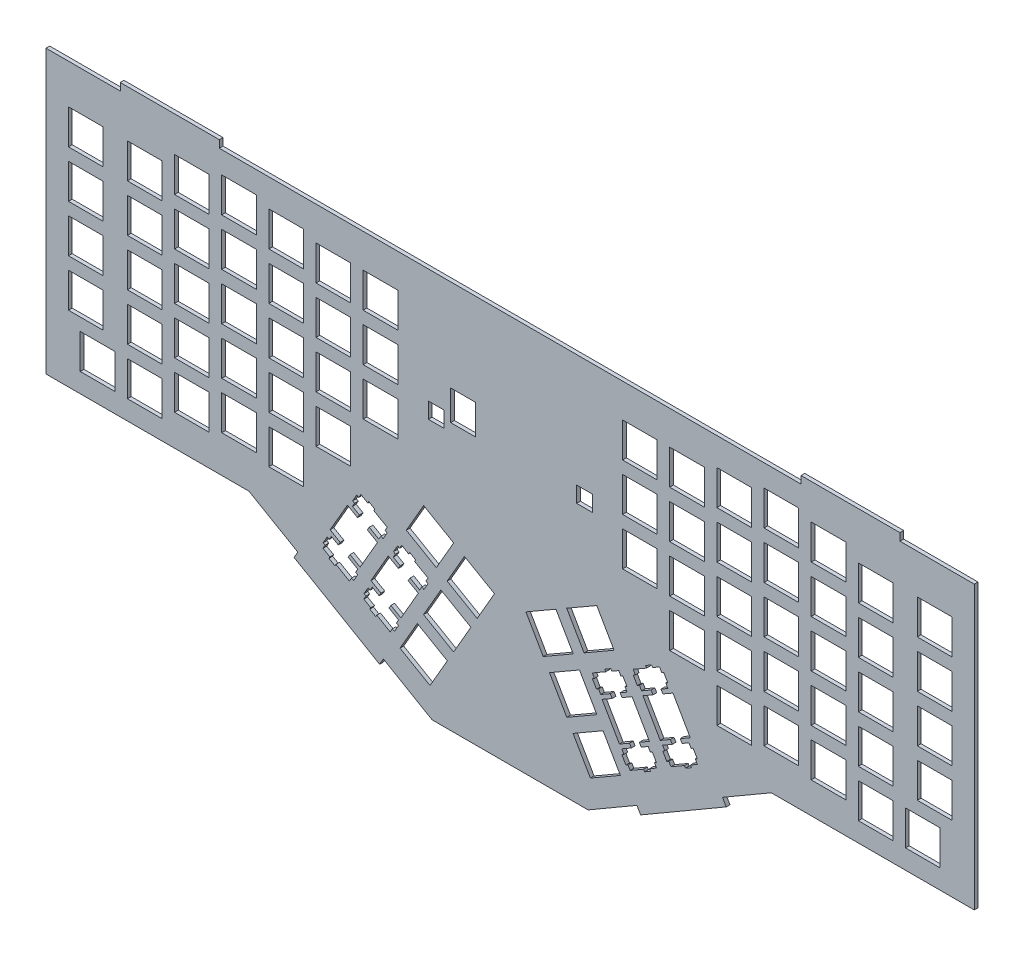
SolidWorks part; units mm, degrees
ref_plane "Front Plane" through (0, 0, 0) normal (0, 0, 1) x (1, 0, 0)
ref_plane "Top Plane" through (0, 0, 0) normal (0, 1, 0) x (1, 0, 0)
ref_plane "Right Plane" through (0, 0, 0) normal (1, 0, 0) x (0, 0, -1)
sketch "Model" plane through (0, 0, 0) normal (0, 0, 1) x (1, 0, 0)
  line L0 (0.0951, 142.78) -> (371.57, 142.78)
  line L1 (371.57, 142.78) -> (371.57, 0.2467)
  line L2 (371.57, 0.2467) -> (0.0951, 0.2467)
  line L3 (0.0951, 0.2467) -> (0.0951, 142.78)
  line L4 (141.314, 10.6977) -> (153.439, 3.6973)
  line L5 (153.439, 3.6973) -> (160.438, 15.8213)
  line L6 (160.438, 15.8213) -> (148.314, 22.8217)
  line L7 (148.314, 22.8217) -> (141.314, 10.6977)
  line L8 (211.224, 15.8213) -> (218.225, 3.6973)
  line L9 (218.225, 3.6973) -> (230.35, 10.6977)
  line L10 (230.35, 10.6977) -> (223.35, 22.8217)
  line L11 (223.35, 22.8217) -> (211.224, 15.8213)
  line L12 (141.126, 45.533) -> (140.33, 45.992)
  line L13 (140.33, 45.992) -> (138.679, 43.1341)
  line L14 (138.679, 43.1341) -> (139.477, 42.6752)
  line L15 (139.477, 42.6752) -> (138.614, 41.1812)
  line L16 (138.614, 41.1812) -> (141.412, 39.5661)
  line L17 (141.412, 39.5661) -> (140.648, 38.2461)
  line L18 (140.648, 38.2461) -> (136.579, 40.5955)
  line L19 (136.579, 40.5955) -> (129.578, 28.4716)
  line L20 (129.578, 28.4716) -> (133.649, 26.1221)
  line L21 (133.649, 26.1221) -> (132.887, 24.8006)
  line L22 (132.887, 24.8006) -> (130.09, 26.4156)
  line L23 (130.09, 26.4156) -> (129.227, 24.9218)
  line L24 (129.227, 24.9218) -> (128.429, 25.3821)
  line L25 (128.429, 25.3821) -> (126.78, 22.524)
  line L26 (126.78, 22.524) -> (127.576, 22.0638)
  line L27 (127.576, 22.0638) -> (126.715, 20.57)
  line L28 (126.715, 20.57) -> (129.512, 18.9549)
  line L29 (129.512, 18.9549) -> (129.099, 18.2411)
  line L30 (129.099, 18.2411) -> (131.524, 16.841)
  line L31 (131.524, 16.841) -> (131.936, 17.5548)
  line L32 (131.936, 17.5548) -> (137.367, 14.4198)
  line L33 (137.367, 14.4198) -> (138.228, 15.9136)
  line L34 (138.228, 15.9136) -> (139.077, 15.423)
  line L35 (139.077, 15.423) -> (140.728, 18.2811)
  line L36 (140.728, 18.2811) -> (139.879, 18.773)
  line L37 (139.879, 18.773) -> (140.742, 20.2654)
  line L38 (140.742, 20.2654) -> (136.871, 22.5006)
  line L39 (136.871, 22.5006) -> (137.633, 23.8221)
  line L40 (137.633, 23.8221) -> (141.702, 21.4712)
  line L41 (141.702, 21.4712) -> (148.703, 33.5952)
  line L42 (148.703, 33.5952) -> (144.632, 35.9463)
  line L43 (144.632, 35.9463) -> (145.396, 37.2664)
  line L44 (145.396, 37.2664) -> (149.266, 35.0311)
  line L45 (149.266, 35.0311) -> (150.129, 36.5248)
  line L46 (150.129, 36.5248) -> (150.978, 36.0345)
  line L47 (150.978, 36.0345) -> (152.628, 38.8923)
  line L48 (152.628, 38.8923) -> (151.778, 39.3831)
  line L49 (151.778, 39.3831) -> (152.641, 40.8767)
  line L50 (152.641, 40.8767) -> (147.212, 44.0119)
  line L51 (147.212, 44.0119) -> (147.624, 44.7269)
  line L52 (147.624, 44.7269) -> (145.198, 46.1271)
  line L53 (145.198, 46.1271) -> (144.786, 45.412)
  line L54 (144.786, 45.412) -> (141.989, 47.027)
  line L55 (141.989, 47.027) -> (141.126, 45.533)
  line L56 (226.876, 45.412) -> (226.464, 46.1271)
  line L57 (226.464, 46.1271) -> (224.04, 44.7269)
  line L58 (224.04, 44.7269) -> (224.452, 44.0119)
  line L59 (224.452, 44.0119) -> (219.021, 40.8767)
  line L60 (219.021, 40.8767) -> (219.884, 39.3831)
  line L61 (219.884, 39.3831) -> (219.035, 38.8923)
  line L62 (219.035, 38.8923) -> (220.686, 36.0345)
  line L63 (220.686, 36.0345) -> (221.535, 36.5248)
  line L64 (221.535, 36.5248) -> (222.396, 35.0311)
  line L65 (222.396, 35.0311) -> (226.267, 37.2664)
  line L66 (226.267, 37.2664) -> (227.031, 35.9463)
  line L67 (227.031, 35.9463) -> (222.961, 33.5952)
  line L68 (222.961, 33.5952) -> (229.96, 21.4712)
  line L69 (229.96, 21.4712) -> (234.031, 23.8221)
  line L70 (234.031, 23.8221) -> (234.793, 22.5006)
  line L71 (234.793, 22.5006) -> (230.922, 20.2654)
  line L72 (230.922, 20.2654) -> (231.785, 18.773)
  line L73 (231.785, 18.773) -> (230.936, 18.2811)
  line L74 (230.936, 18.2811) -> (232.585, 15.423)
  line L75 (232.585, 15.423) -> (233.434, 15.9136)
  line L76 (233.434, 15.9136) -> (234.297, 14.4198)
  line L77 (234.297, 14.4198) -> (239.726, 17.5548)
  line L78 (239.726, 17.5548) -> (240.14, 16.841)
  line L79 (240.14, 16.841) -> (242.565, 18.2411)
  line L80 (242.565, 18.2411) -> (242.152, 18.9549)
  line L81 (242.152, 18.9549) -> (244.949, 20.57)
  line L82 (244.949, 20.57) -> (244.086, 22.0638)
  line L83 (244.086, 22.0638) -> (244.883, 22.524)
  line L84 (244.883, 22.524) -> (243.233, 25.3821)
  line L85 (243.233, 25.3821) -> (242.437, 24.9218)
  line L86 (242.437, 24.9218) -> (241.573, 26.4156)
  line L87 (241.573, 26.4156) -> (238.777, 24.8006)
  line L88 (238.777, 24.8006) -> (238.014, 26.1221)
  line L89 (238.014, 26.1221) -> (242.084, 28.4716)
  line L90 (242.084, 28.4716) -> (235.085, 40.5955)
  line L91 (235.085, 40.5955) -> (231.014, 38.2461)
  line L92 (231.014, 38.2461) -> (230.251, 39.5661)
  line L93 (230.251, 39.5661) -> (233.048, 41.1812)
  line L94 (233.048, 41.1812) -> (232.187, 42.6752)
  line L95 (232.187, 42.6752) -> (232.984, 43.1341)
  line L96 (232.984, 43.1341) -> (231.334, 45.992)
  line L97 (231.334, 45.992) -> (230.536, 45.533)
  line L98 (230.536, 45.533) -> (229.674, 47.027)
  line L99 (229.674, 47.027) -> (226.876, 45.412)
  line L100 (150.839, 27.1942) -> (162.964, 20.1952)
  line L101 (162.964, 20.1952) -> (169.963, 32.3191)
  line L102 (169.963, 32.3191) -> (157.839, 39.3196)
  line L103 (157.839, 39.3196) -> (150.839, 27.1942)
  line L104 (201.699, 32.3191) -> (208.7, 20.1952)
  line L105 (208.7, 20.1952) -> (220.825, 27.1942)
  line L106 (220.825, 27.1942) -> (213.825, 39.3196)
  line L107 (213.825, 39.3196) -> (201.699, 32.3191)
  line L108 (124.627, 55.058) -> (123.832, 55.517)
  line L109 (123.832, 55.517) -> (122.182, 52.6591)
  line L110 (122.182, 52.6591) -> (122.979, 52.2002)
  line L111 (122.979, 52.2002) -> (122.116, 50.7062)
  line L112 (122.116, 50.7062) -> (124.912, 49.0911)
  line L113 (124.912, 49.0911) -> (124.15, 47.7711)
  line L114 (124.15, 47.7711) -> (120.081, 50.1206)
  line L115 (120.081, 50.1206) -> (113.08, 37.9966)
  line L116 (113.08, 37.9966) -> (117.151, 35.6471)
  line L117 (117.151, 35.6471) -> (116.389, 34.3256)
  line L118 (116.389, 34.3256) -> (113.592, 35.9406)
  line L119 (113.592, 35.9406) -> (112.729, 34.4468)
  line L120 (112.729, 34.4468) -> (111.933, 34.9071)
  line L121 (111.933, 34.9071) -> (110.283, 32.0491)
  line L122 (110.283, 32.0491) -> (111.078, 31.5888)
  line L123 (111.078, 31.5888) -> (110.217, 30.095)
  line L124 (110.217, 30.095) -> (113.013, 28.4799)
  line L125 (113.013, 28.4799) -> (112.601, 27.7661)
  line L126 (112.601, 27.7661) -> (115.025, 26.366)
  line L127 (115.025, 26.366) -> (115.438, 27.0798)
  line L128 (115.438, 27.0798) -> (120.869, 23.9448)
  line L129 (120.869, 23.9448) -> (121.731, 25.4386)
  line L130 (121.731, 25.4386) -> (122.579, 24.948)
  line L131 (122.579, 24.948) -> (124.229, 27.806)
  line L132 (124.229, 27.806) -> (123.38, 28.2966)
  line L133 (123.38, 28.2966) -> (124.244, 29.7904)
  line L134 (124.244, 29.7904) -> (120.373, 32.0256)
  line L135 (120.373, 32.0256) -> (121.135, 33.3471)
  line L136 (121.135, 33.3471) -> (125.204, 30.9962)
  line L137 (125.204, 30.9962) -> (132.205, 43.12)
  line L138 (132.205, 43.12) -> (128.134, 45.4713)
  line L139 (128.134, 45.4713) -> (128.898, 46.7914)
  line L140 (128.898, 46.7914) -> (132.769, 44.5562)
  line L141 (132.769, 44.5562) -> (133.631, 46.0498)
  line L142 (133.631, 46.0498) -> (134.48, 45.5595)
  line L143 (134.48, 45.5595) -> (136.13, 48.4173)
  line L144 (136.13, 48.4173) -> (135.281, 48.9081)
  line L145 (135.281, 48.9081) -> (136.143, 50.4017)
  line L146 (136.143, 50.4017) -> (130.714, 53.5368)
  line L147 (130.714, 53.5368) -> (131.126, 54.2519)
  line L148 (131.126, 54.2519) -> (128.702, 55.6521)
  line L149 (128.702, 55.6521) -> (128.288, 54.937)
  line L150 (128.288, 54.937) -> (125.491, 56.552)
  line L151 (125.491, 56.552) -> (124.627, 55.058)
  line L152 (243.374, 54.937) -> (242.962, 55.6521)
  line L153 (242.962, 55.6521) -> (240.538, 54.2519)
  line L154 (240.538, 54.2519) -> (240.95, 53.5368)
  line L155 (240.95, 53.5368) -> (235.519, 50.4017)
  line L156 (235.519, 50.4017) -> (236.383, 48.9081)
  line L157 (236.383, 48.9081) -> (235.533, 48.4173)
  line L158 (235.533, 48.4173) -> (237.184, 45.5595)
  line L159 (237.184, 45.5595) -> (238.033, 46.0498)
  line L160 (238.033, 46.0498) -> (238.894, 44.5562)
  line L161 (238.894, 44.5562) -> (242.765, 46.7914)
  line L162 (242.765, 46.7914) -> (243.528, 45.4713)
  line L163 (243.528, 45.4713) -> (239.457, 43.12)
  line L164 (239.457, 43.12) -> (246.458, 30.9962)
  line L165 (246.458, 30.9962) -> (250.527, 33.3471)
  line L166 (250.527, 33.3471) -> (251.291, 32.0256)
  line L167 (251.291, 32.0256) -> (247.42, 29.7904)
  line L168 (247.42, 29.7904) -> (248.283, 28.2966)
  line L169 (248.283, 28.2966) -> (247.434, 27.806)
  line L170 (247.434, 27.806) -> (249.083, 24.948)
  line L171 (249.083, 24.948) -> (249.932, 25.4386)
  line L172 (249.932, 25.4386) -> (250.795, 23.9448)
  line L173 (250.795, 23.9448) -> (256.224, 27.0798)
  line L174 (256.224, 27.0798) -> (256.638, 26.366)
  line L175 (256.638, 26.366) -> (259.062, 27.7661)
  line L176 (259.062, 27.7661) -> (258.65, 28.4799)
  line L177 (258.65, 28.4799) -> (261.447, 30.095)
  line L178 (261.447, 30.095) -> (260.584, 31.5888)
  line L179 (260.584, 31.5888) -> (261.381, 32.0491)
  line L180 (261.381, 32.0491) -> (259.73, 34.9071)
  line L181 (259.73, 34.9071) -> (258.935, 34.4468)
  line L182 (258.935, 34.4468) -> (258.072, 35.9406)
  line L183 (258.072, 35.9406) -> (255.275, 34.3256)
  line L184 (255.275, 34.3256) -> (254.51, 35.6471)
  line L185 (254.51, 35.6471) -> (258.582, 37.9966)
  line L186 (258.582, 37.9966) -> (251.583, 50.1206)
  line L187 (251.583, 50.1206) -> (247.512, 47.7711)
  line L188 (247.512, 47.7711) -> (246.75, 49.0911)
  line L189 (246.75, 49.0911) -> (249.546, 50.7062)
  line L190 (249.546, 50.7062) -> (248.685, 52.2002)
  line L191 (248.685, 52.2002) -> (249.48, 52.6591)
  line L192 (249.48, 52.6591) -> (247.831, 55.517)
  line L193 (247.831, 55.517) -> (247.034, 55.058)
  line L194 (247.034, 55.058) -> (246.172, 56.552)
  line L195 (246.172, 56.552) -> (243.374, 54.937)
  line L196 (160.364, 43.6922) -> (172.489, 36.6931)
  line L197 (172.489, 36.6931) -> (179.488, 48.817)
  line L198 (179.488, 48.817) -> (167.364, 55.8176)
  line L199 (167.364, 55.8176) -> (160.364, 43.6922)
  line L200 (192.174, 48.817) -> (199.175, 36.6931)
  line L201 (199.175, 36.6931) -> (211.3, 43.6922)
  line L202 (211.3, 43.6922) -> (204.3, 55.8176)
  line L203 (204.3, 55.8176) -> (192.174, 48.817)
  line L204 (12.1447, 56.9129) -> (26.1441, 56.9129)
  line L205 (26.1441, 56.9129) -> (26.1441, 42.9122)
  line L206 (26.1441, 42.9122) -> (12.1447, 42.9122)
  line L207 (12.1447, 42.9122) -> (12.1447, 56.9129)
  line L208 (31.1947, 56.9129) -> (45.194, 56.9129)
  line L209 (45.194, 56.9129) -> (45.194, 42.9122)
  line L210 (45.194, 42.9122) -> (31.1947, 42.9122)
  line L211 (31.1947, 42.9122) -> (31.1947, 56.9129)
  line L212 (326.47, 56.9129) -> (340.469, 56.9129)
  line L213 (340.469, 56.9129) -> (340.469, 42.9122)
  line L214 (340.469, 42.9122) -> (326.47, 42.9122)
  line L215 (326.47, 42.9122) -> (326.47, 56.9129)
  line L216 (345.52, 56.9129) -> (359.519, 56.9129)
  line L217 (359.519, 56.9129) -> (359.519, 42.9122)
  line L218 (359.519, 42.9122) -> (345.52, 42.9122)
  line L219 (345.52, 42.9122) -> (345.52, 56.9129)
  line L220 (143.866, 53.2172) -> (155.991, 46.2181)
  line L221 (155.991, 46.2181) -> (162.99, 58.342)
  line L222 (162.99, 58.342) -> (150.865, 65.3426)
  line L223 (150.865, 65.3426) -> (143.866, 53.2172)
  line L224 (208.672, 58.342) -> (215.672, 46.2181)
  line L225 (215.672, 46.2181) -> (227.798, 53.2172)
  line L226 (227.798, 53.2172) -> (220.798, 65.3426)
  line L227 (220.798, 65.3426) -> (208.672, 58.342)
  line L228 (50.2447, 61.674) -> (64.244, 61.674)
  line L229 (64.244, 61.674) -> (64.244, 47.6747)
  line L230 (64.244, 47.6747) -> (50.2447, 47.6747)
  line L231 (50.2447, 47.6747) -> (50.2447, 61.674)
  line L232 (88.3447, 61.674) -> (102.344, 61.674)
  line L233 (102.344, 61.674) -> (102.344, 47.6747)
  line L234 (102.344, 47.6747) -> (88.3447, 47.6747)
  line L235 (88.3447, 47.6747) -> (88.3447, 61.674)
  line L236 (269.32, 61.674) -> (283.319, 61.674)
  line L237 (283.319, 61.674) -> (283.319, 47.6747)
  line L238 (283.319, 47.6747) -> (269.32, 47.6747)
  line L239 (269.32, 47.6747) -> (269.32, 61.674)
  line L240 (307.42, 61.674) -> (321.419, 61.674)
  line L241 (321.419, 61.674) -> (321.419, 47.6747)
  line L242 (321.419, 47.6747) -> (307.42, 47.6747)
  line L243 (307.42, 47.6747) -> (307.42, 61.674)
  line L244 (69.2947, 64.0553) -> (83.294, 64.0553)
  line L245 (83.294, 64.0553) -> (83.294, 50.056)
  line L246 (83.294, 50.056) -> (69.2947, 50.056)
  line L247 (69.2947, 50.056) -> (69.2947, 64.0553)
  line L248 (288.37, 64.0553) -> (302.369, 64.0553)
  line L249 (302.369, 64.0553) -> (302.369, 50.056)
  line L250 (302.369, 50.056) -> (288.37, 50.056)
  line L251 (288.37, 50.056) -> (288.37, 64.0553)
  line L252 (7.3822, 75.9629) -> (21.3817, 75.9629)
  line L253 (21.3817, 75.9629) -> (21.3817, 61.9622)
  line L254 (21.3817, 61.9622) -> (7.3822, 61.9622)
  line L255 (7.3822, 61.9622) -> (7.3822, 75.9629)
  line L256 (31.1947, 75.9629) -> (45.194, 75.9629)
  line L257 (45.194, 75.9629) -> (45.194, 61.9622)
  line L258 (45.194, 61.9622) -> (31.1947, 61.9622)
  line L259 (31.1947, 61.9622) -> (31.1947, 75.9629)
  line L260 (326.47, 75.9629) -> (340.469, 75.9629)
  line L261 (340.469, 75.9629) -> (340.469, 61.9622)
  line L262 (340.469, 61.9622) -> (326.47, 61.9622)
  line L263 (326.47, 61.9622) -> (326.47, 75.9629)
  line L264 (350.282, 75.9629) -> (364.282, 75.9629)
  line L265 (364.282, 75.9629) -> (364.282, 61.9622)
  line L266 (364.282, 61.9622) -> (350.282, 61.9622)
  line L267 (350.282, 61.9622) -> (350.282, 75.9629)
  line L268 (107.395, 78.3428) -> (121.394, 78.3428)
  line L269 (121.394, 78.3428) -> (121.394, 64.3435)
  line L270 (121.394, 64.3435) -> (107.395, 64.3435)
  line L271 (107.395, 64.3435) -> (107.395, 78.3428)
  line L272 (250.27, 78.3428) -> (264.269, 78.3428)
  line L273 (264.269, 78.3428) -> (264.269, 64.3435)
  line L274 (264.269, 64.3435) -> (250.27, 64.3435)
  line L275 (250.27, 64.3435) -> (250.27, 78.3428)
  line L276 (50.2447, 80.724) -> (64.244, 80.724)
  line L277 (64.244, 80.724) -> (64.244, 66.7247)
  line L278 (64.244, 66.7247) -> (50.2447, 66.7247)
  line L279 (50.2447, 66.7247) -> (50.2447, 80.724)
  line L280 (88.3447, 80.724) -> (102.344, 80.724)
  line L281 (102.344, 80.724) -> (102.344, 66.7247)
  line L282 (102.344, 66.7247) -> (88.3447, 66.7247)
  line L283 (88.3447, 66.7247) -> (88.3447, 80.724)
  line L284 (269.32, 80.724) -> (283.319, 80.724)
  line L285 (283.319, 80.724) -> (283.319, 66.7247)
  line L286 (283.319, 66.7247) -> (269.32, 66.7247)
  line L287 (269.32, 66.7247) -> (269.32, 80.724)
  line L288 (307.42, 80.724) -> (321.419, 80.724)
  line L289 (321.419, 80.724) -> (321.419, 66.7247)
  line L290 (321.419, 66.7247) -> (307.42, 66.7247)
  line L291 (307.42, 66.7247) -> (307.42, 80.724)
  line L292 (69.2947, 83.1053) -> (83.294, 83.1053)
  line L293 (83.294, 83.1053) -> (83.294, 69.106)
  line L294 (83.294, 69.106) -> (69.2947, 69.106)
  line L295 (69.2947, 69.106) -> (69.2947, 83.1053)
  line L296 (288.37, 83.1053) -> (302.369, 83.1053)
  line L297 (302.369, 83.1053) -> (302.369, 69.106)
  line L298 (302.369, 69.106) -> (288.37, 69.106)
  line L299 (288.37, 69.106) -> (288.37, 83.1053)
  line L300 (7.3822, 95.0129) -> (21.3817, 95.0129)
  line L301 (21.3817, 95.0129) -> (21.3817, 81.0122)
  line L302 (21.3817, 81.0122) -> (7.3822, 81.0122)
  line L303 (7.3822, 81.0122) -> (7.3822, 95.0129)
  line L304 (31.1947, 95.0129) -> (45.194, 95.0129)
  line L305 (45.194, 95.0129) -> (45.194, 81.0122)
  line L306 (45.194, 81.0122) -> (31.1947, 81.0122)
  line L307 (31.1947, 81.0122) -> (31.1947, 95.0129)
  line L308 (326.47, 95.0129) -> (340.469, 95.0129)
  line L309 (340.469, 95.0129) -> (340.469, 81.0122)
  line L310 (340.469, 81.0122) -> (326.47, 81.0122)
  line L311 (326.47, 81.0122) -> (326.47, 95.0129)
  line L312 (350.282, 95.0129) -> (364.282, 95.0129)
  line L313 (364.282, 95.0129) -> (364.282, 81.0122)
  line L314 (364.282, 81.0122) -> (350.282, 81.0122)
  line L315 (350.282, 81.0122) -> (350.282, 95.0129)
  line L316 (107.395, 97.3928) -> (121.394, 97.3928)
  line L317 (121.394, 97.3928) -> (121.394, 83.3935)
  line L318 (121.394, 83.3935) -> (107.395, 83.3935)
  line L319 (107.395, 83.3935) -> (107.395, 97.3928)
  line L320 (126.445, 97.3928) -> (140.444, 97.3928)
  line L321 (140.444, 97.3928) -> (140.444, 83.3935)
  line L322 (140.444, 83.3935) -> (126.445, 83.3935)
  line L323 (126.445, 83.3935) -> (126.445, 97.3928)
  line L324 (231.22, 97.3928) -> (245.219, 97.3928)
  line L325 (245.219, 97.3928) -> (245.219, 83.3935)
  line L326 (245.219, 83.3935) -> (231.22, 83.3935)
  line L327 (231.22, 83.3935) -> (231.22, 97.3928)
  line L328 (250.27, 97.3928) -> (264.269, 97.3928)
  line L329 (264.269, 97.3928) -> (264.269, 83.3935)
  line L330 (264.269, 83.3935) -> (250.27, 83.3935)
  line L331 (250.27, 83.3935) -> (250.27, 97.3928)
  line L332 (50.2447, 99.774) -> (64.244, 99.774)
  line L333 (64.244, 99.774) -> (64.244, 85.7747)
  line L334 (64.244, 85.7747) -> (50.2447, 85.7747)
  line L335 (50.2447, 85.7747) -> (50.2447, 99.774)
  line L336 (88.3447, 99.774) -> (102.344, 99.774)
  line L337 (102.344, 99.774) -> (102.344, 85.7747)
  line L338 (102.344, 85.7747) -> (88.3447, 85.7747)
  line L339 (88.3447, 85.7747) -> (88.3447, 99.774)
  line L340 (269.32, 99.774) -> (283.319, 99.774)
  line L341 (283.319, 99.774) -> (283.319, 85.7747)
  line L342 (283.319, 85.7747) -> (269.32, 85.7747)
  line L343 (269.32, 85.7747) -> (269.32, 99.774)
  line L344 (307.42, 99.774) -> (321.419, 99.774)
  line L345 (321.419, 99.774) -> (321.419, 85.7747)
  line L346 (321.419, 85.7747) -> (307.42, 85.7747)
  line L347 (307.42, 85.7747) -> (307.42, 99.774)
  line L348 (69.2947, 102.155) -> (83.294, 102.155)
  line L349 (83.294, 102.155) -> (83.294, 88.156)
  line L350 (83.294, 88.156) -> (69.2947, 88.156)
  line L351 (69.2947, 88.156) -> (69.2947, 102.155)
  line L352 (288.37, 102.155) -> (302.369, 102.155)
  line L353 (302.369, 102.155) -> (302.369, 88.156)
  line L354 (302.369, 88.156) -> (288.37, 88.156)
  line L355 (288.37, 88.156) -> (288.37, 102.155)
  line L356 (7.3822, 114.063) -> (21.3817, 114.063)
  line L357 (21.3817, 114.063) -> (21.3817, 100.062)
  line L358 (21.3817, 100.062) -> (7.3822, 100.062)
  line L359 (7.3822, 100.062) -> (7.3822, 114.063)
  line L360 (31.1947, 114.063) -> (45.194, 114.063)
  line L361 (45.194, 114.063) -> (45.194, 100.062)
  line L362 (45.194, 100.062) -> (31.1947, 100.062)
  line L363 (31.1947, 100.062) -> (31.1947, 114.063)
  line L364 (326.47, 114.063) -> (340.469, 114.063)
  line L365 (340.469, 114.063) -> (340.469, 100.062)
  line L366 (340.469, 100.062) -> (326.47, 100.062)
  line L367 (326.47, 100.062) -> (326.47, 114.063)
  line L368 (350.282, 114.063) -> (364.282, 114.063)
  line L369 (364.282, 114.063) -> (364.282, 100.062)
  line L370 (364.282, 100.062) -> (350.282, 100.062)
  line L371 (350.282, 100.062) -> (350.282, 114.063)
  line L372 (107.395, 116.443) -> (121.394, 116.443)
  line L373 (121.394, 116.443) -> (121.394, 102.443)
  line L374 (121.394, 102.443) -> (107.395, 102.443)
  line L375 (107.395, 102.443) -> (107.395, 116.443)
  line L376 (126.445, 116.443) -> (140.444, 116.443)
  line L377 (140.444, 116.443) -> (140.444, 102.443)
  line L378 (140.444, 102.443) -> (126.445, 102.443)
  line L379 (126.445, 102.443) -> (126.445, 116.443)
  line L380 (231.22, 116.443) -> (245.219, 116.443)
  line L381 (245.219, 116.443) -> (245.219, 102.443)
  line L382 (245.219, 102.443) -> (231.22, 102.443)
  line L383 (231.22, 102.443) -> (231.22, 116.443)
  line L384 (250.27, 116.443) -> (264.269, 116.443)
  line L385 (264.269, 116.443) -> (264.269, 102.443)
  line L386 (264.269, 102.443) -> (250.27, 102.443)
  line L387 (250.27, 102.443) -> (250.27, 116.443)
  line L388 (50.2447, 118.824) -> (64.244, 118.824)
  line L389 (64.244, 118.824) -> (64.244, 104.825)
  line L390 (64.244, 104.825) -> (50.2447, 104.825)
  line L391 (50.2447, 104.825) -> (50.2447, 118.824)
  line L392 (88.3447, 118.824) -> (102.344, 118.824)
  line L393 (102.344, 118.824) -> (102.344, 104.825)
  line L394 (102.344, 104.825) -> (88.3447, 104.825)
  line L395 (88.3447, 104.825) -> (88.3447, 118.824)
  line L396 (269.32, 118.824) -> (283.319, 118.824)
  line L397 (283.319, 118.824) -> (283.319, 104.825)
  line L398 (283.319, 104.825) -> (269.32, 104.825)
  line L399 (269.32, 104.825) -> (269.32, 118.824)
  line L400 (307.42, 118.824) -> (321.419, 118.824)
  line L401 (321.419, 118.824) -> (321.419, 104.825)
  line L402 (321.419, 104.825) -> (307.42, 104.825)
  line L403 (307.42, 104.825) -> (307.42, 118.824)
  line L404 (69.2947, 121.205) -> (83.294, 121.205)
  line L405 (83.294, 121.205) -> (83.294, 107.206)
  line L406 (83.294, 107.206) -> (69.2947, 107.206)
  line L407 (69.2947, 107.206) -> (69.2947, 121.205)
  line L408 (288.37, 121.205) -> (302.369, 121.205)
  line L409 (302.369, 121.205) -> (302.369, 107.206)
  line L410 (302.369, 107.206) -> (288.37, 107.206)
  line L411 (288.37, 107.206) -> (288.37, 121.205)
  line L412 (7.3822, 133.113) -> (21.3817, 133.113)
  line L413 (21.3817, 133.113) -> (21.3817, 119.112)
  line L414 (21.3817, 119.112) -> (7.3822, 119.112)
  line L415 (7.3822, 119.112) -> (7.3822, 133.113)
  line L416 (31.1947, 133.113) -> (45.194, 133.113)
  line L417 (45.194, 133.113) -> (45.194, 119.112)
  line L418 (45.194, 119.112) -> (31.1947, 119.112)
  line L419 (31.1947, 119.112) -> (31.1947, 133.113)
  line L420 (326.47, 133.113) -> (340.469, 133.113)
  line L421 (340.469, 133.113) -> (340.469, 119.112)
  line L422 (340.469, 119.112) -> (326.47, 119.112)
  line L423 (326.47, 119.112) -> (326.47, 133.113)
  line L424 (350.282, 133.113) -> (364.282, 133.113)
  line L425 (364.282, 133.113) -> (364.282, 119.112)
  line L426 (364.282, 119.112) -> (350.282, 119.112)
  line L427 (350.282, 119.112) -> (350.282, 133.113)
  line L428 (107.395, 135.493) -> (121.394, 135.493)
  line L429 (121.394, 135.493) -> (121.394, 121.493)
  line L430 (121.394, 121.493) -> (107.395, 121.493)
  line L431 (107.395, 121.493) -> (107.395, 135.493)
  line L432 (126.445, 135.493) -> (140.444, 135.493)
  line L433 (140.444, 135.493) -> (140.444, 121.493)
  line L434 (140.444, 121.493) -> (126.445, 121.493)
  line L435 (126.445, 121.493) -> (126.445, 135.493)
  line L436 (231.22, 135.493) -> (245.219, 135.493)
  line L437 (245.219, 135.493) -> (245.219, 121.493)
  line L438 (245.219, 121.493) -> (231.22, 121.493)
  line L439 (231.22, 121.493) -> (231.22, 135.493)
  line L440 (250.27, 135.493) -> (264.269, 135.493)
  line L441 (264.269, 135.493) -> (264.269, 121.493)
  line L442 (264.269, 121.493) -> (250.27, 121.493)
  line L443 (250.27, 121.493) -> (250.27, 135.493)
  line L444 (50.2447, 137.874) -> (64.244, 137.874)
  line L445 (64.244, 137.874) -> (64.244, 123.875)
  line L446 (64.244, 123.875) -> (50.2447, 123.875)
  line L447 (50.2447, 123.875) -> (50.2447, 137.874)
  line L448 (88.3447, 137.874) -> (102.344, 137.874)
  line L449 (102.344, 137.874) -> (102.344, 123.875)
  line L450 (102.344, 123.875) -> (88.3447, 123.875)
  line L451 (88.3447, 123.875) -> (88.3447, 137.874)
  line L452 (269.32, 137.874) -> (283.319, 137.874)
  line L453 (283.319, 137.874) -> (283.319, 123.875)
  line L454 (283.319, 123.875) -> (269.32, 123.875)
  line L455 (269.32, 123.875) -> (269.32, 137.874)
  line L456 (307.42, 137.874) -> (321.419, 137.874)
  line L457 (321.419, 137.874) -> (321.419, 123.875)
  line L458 (321.419, 123.875) -> (307.42, 123.875)
  line L459 (307.42, 123.875) -> (307.42, 137.874)
  line L460 (69.2947, 140.255) -> (83.294, 140.255)
  line L461 (83.294, 140.255) -> (83.294, 126.256)
  line L462 (83.294, 126.256) -> (69.2947, 126.256)
  line L463 (69.2947, 126.256) -> (69.2947, 140.255)
  line L464 (288.37, 140.255) -> (302.369, 140.255)
  line L465 (302.369, 140.255) -> (302.369, 126.256)
  line L466 (302.369, 126.256) -> (288.37, 126.256)
  line L467 (288.37, 126.256) -> (288.37, 140.255)
extrude "Boss-Extrude1" add sketch "Model" along normal blind 1.5
sketch "Sketch1" plane through (0, 142.78, 0) normal (0, 1, 0) x (1, 0, 0)
  line L0 (0.0951, 0) -> (0.0951, -1.5)
  line L1 (0.0951, -1.5) -> (371.57, -1.5)
  line L2 (371.57, -1.5) -> (371.57, 0)
  line L3 (371.57, 0) -> (0.0951, 0)
  line L4 (0.0951, -1.5) -> (0.0951, 0) construction
extrude "Boss-Extrude2" add sketch "Sketch1" along normal blind 5.46
sketch "Sketch2" plane through (0, 0.2467, 0) normal (0, -1, 0) x (1, 0, 0)
  line L0 (0.0951, 1.5) -> (0.0951, 0)
  line L1 (0.0951, 0) -> (371.57, 0)
  line L2 (371.57, 0) -> (371.57, 1.5)
  line L3 (371.57, 1.5) -> (0.0951, 1.5)
extrude "Boss-Extrude3" add sketch "Sketch2" along normal blind 8.2
sketch "Sketch6" plane through (371.57, 0, 0) normal (1, 0, 0) x (0, 0, -1)
  line L0 (-1.5, -7.9533) -> (0, -7.9533)
  line L1 (0, -7.9533) -> (0, 148.24)
  line L2 (0, 148.24) -> (-1.5, 148.24)
  line L3 (-1.5, 148.24) -> (-1.5, -7.9533)
extrude "Boss-Extrude5" add sketch "Sketch6" along normal blind 2
sketch "Sketch9" plane through (0.0951, 0, 0) normal (-1, 0, 0) x (0, 0, 1)
  line L0 (0, -7.9533) -> (1.5, -7.9533)
  line L1 (1.5, -7.9533) -> (1.5, 148.24)
  line L2 (1.5, 148.24) -> (0, 148.24)
  line L4 (0, 148.24) -> (0, -7.9533)
extrude "Boss-Extrude8" add sketch "Sketch9" along normal blind 10
sketch "Sketch7" plane through (0, 148.24, 0) normal (0, 1, 0) x (1, 0, 0)
  line L0 (-9.9049, 0) -> (-9.9049, -1.5)
  line L1 (-9.9049, -1.5) -> (373.57, -1.5)
  line L2 (373.57, -1.5) -> (373.57, 0)
  line L3 (373.57, 0) -> (-9.9049, 0)
  line L4 (373.57, 0) -> (-9.9049, 0) construction
extrude "Boss-Extrude9" add sketch "Sketch7" along normal blind 10
sketch "Sketch10" plane through (0, 0, 0) normal (0, 0, -1) x (-1, 0, 0)
  line L9 (9.9049, -7.9533) -> (9.9049, 158.24)
  line L10 (9.9049, 158.24) -> (-373.57, 158.24)
  line L11 (-373.57, 158.24) -> (-373.57, 149.0988)
  line L12 (-373.57, -7.9533) -> (-373.57, 158.24) construction
  line L13 (-373.57, 149.0988) -> (-373.3117, 149.0988) construction
  line L14 (-373.3117, 149.0988) -> (1.6883, 149.0988)
  line L15 (9.9049, -7.9533) -> (-373.57, -7.9533) construction
  line L17 (1.6883, 149.0988) -> (1.6883, 35.0988)
  line L18 (1.6883, 35.0988) -> (-80.3117, 35.0988)
  line L19 (-80.3117, 35.0988) -> (-154.3117, -7.9012)
  line L20 (-154.3117, -7.9012) -> (-154.3117, -7.9533) construction
  line L21 (-154.3117, -7.9533) -> (9.9049, -7.9533)
  line L22 (-154.3117, -7.9533) -> (-373.57, -7.9533)
  line L23 (-373.57, -7.9533) -> (-373.57, 149.0988)
  line L24 (-373.3117, 149.0988) -> (-373.3117, 35.0988)
  line L25 (-373.3117, 35.0988) -> (-291.3117, 35.0988)
  line L26 (-291.3117, 35.0988) -> (-217.3117, -7.9012)
  line L27 (-291.3117, 35.0988) -> (-217.3117, -7.9012) construction
  line L28 (-217.3117, -7.9012) -> (-154.3117, -7.9012) construction
  line L29 (-217.3117, -7.9012) -> (-154.3117, -7.9012)
extrude "Cut-Extrude1" cut sketch "Sketch10" against normal blind 10
sketch "Sketch4" plane through (0, 0, 1.5) normal (0, 0, 1) x (1, 0, 0)
  line L0 (158.9617, 99.6888) -> (159.1617, 99.6888) construction
  line L1 (152.7617, 102.8888) -> (159.1617, 102.8888)
  line L2 (152.7617, 102.8888) -> (152.7617, 96.4888)
  line L3 (152.7617, 96.4888) -> (159.1617, 96.4888)
  line L4 (159.1617, 102.8888) -> (159.1617, 96.4888)
  line L5 (155.9617, 96.4888) -> (155.9617, 102.8888) construction
  line L6 (152.7617, 99.6888) -> (159.1617, 99.6888) construction
  line L7 (218.8617, 100.2388) -> (219.0617, 100.2388) construction
  line L8 (155.9617, 102.6888) -> (155.9617, 102.8888) construction
  line L9 (218.8617, 97.5388) -> (218.8617, 102.9388) construction
  line L10 (165.7807, 109.9588) -> (167.8127, 109.9588) construction
  line L11 (166.7967, 109.9588) -> (166.7967, 111.9588) construction
  line L12 (161.7967, 111.9588) -> (171.7967, 111.9588)
  line L13 (161.7967, 111.9588) -> (161.7967, 99.8388)
  line L14 (161.7967, 99.8388) -> (171.7967, 99.8388)
  line L15 (171.7967, 111.9588) -> (171.7967, 99.8388)
  line L16 (161.7967, 111.9588) -> (171.7967, 99.8388) construction
  line L17 (161.7967, 99.8388) -> (171.7967, 111.9588) construction
  line L18 (166.7967, 102.3388) -> (166.7967, 99.8388) construction
  line L19 (215.8617, 103.2388) -> (215.8617, 103.4432) construction
  line L20 (212.6617, 103.4432) -> (219.0617, 103.4432)
  line L21 (212.6617, 103.4432) -> (212.6617, 97.0344)
  line L22 (212.6617, 97.0344) -> (219.0617, 97.0344)
  line L23 (219.0617, 103.4432) -> (219.0617, 97.0344)
  line L24 (212.6617, 103.4432) -> (219.0617, 97.0344) construction
  line L25 (212.6617, 97.0344) -> (219.0617, 103.4432) construction
  line L26 (218.5617, 103.2388) -> (213.1617, 103.2388) construction
  line L27 (158.9617, 96.9888) -> (158.9617, 102.3888) construction
  line L30 (158.6617, 102.6888) -> (153.2617, 102.6888) construction
  point P12 (166.7967, 105.8988)
  point P21 (215.8617, 100.2388)
  point P152 (155.9617, 99.6888)
  dimension "D1" = 0.2
  dimension "D2" = 0.2
  dimension "D3" = 2
  dimension "D4" = 2.5
  dimension "D5" = 10
  dimension "D6" = 0.2
  dimension "D7" = 0.2044
extrude "Cut-Extrude2" cut sketch "Sketch4" against normal blind 2
sketch "Sketch11" plane through (0, 149.0988, 0) normal (0, 1, 0) x (1, 0, 0)
  line L0 (-1.6883, 0) -> (28.3117, 0) construction
  line L1 (-1.6883, 0) -> (373.3117, 0) construction
  line L2 (28.3117, 0) -> (28.3117, -1.5)
  line L3 (-1.6883, -1.5) -> (373.3117, -1.5) construction
  line L4 (28.3117, -1.5) -> (68.3117, -1.5)
  line L5 (68.3117, -1.5) -> (68.3117, 0)
  line L6 (68.3117, 0) -> (28.3117, 0)
  line L7 (373.3117, 0) -> (343.3117, 0) construction
  line L8 (373.3117, -1.5) -> (373.3117, 0) construction
  line L9 (343.3117, 0) -> (343.3117, -1.5)
  line L10 (343.3117, -1.5) -> (303.3117, -1.5)
  line L11 (303.3117, -1.5) -> (303.3117, 0)
  line L12 (303.3117, 0) -> (343.3117, 0)
  dimension "D1" = 30
  dimension "D2" = 40
  dimension "D3" = 30
  dimension "D4" = 40
extrude "Boss-Extrude10" add sketch "Sketch11" along normal blind 3
sketch "Sketch13" plane through (35.5196, 61.1267, 0) normal (-0.5024, -0.8646, 0) x (0.8646, -0.5024, 0)
  line L0 (94.5984, 1.5) -> (114.5984, 1.5)
  line L1 (137.3915, 1.5) -> (51.8053, 1.5) construction
  line L2 (114.5984, 1.5) -> (114.5984, 0)
  line L3 (137.3915, 0) -> (51.8053, 0) construction
  line L4 (114.5984, 0) -> (74.5984, 0)
  line L5 (74.5984, 0) -> (74.5984, 1.5)
  line L6 (74.5984, 1.5) -> (94.5984, 1.5)
  dimension "D1" = 40
extrude "Boss-Extrude11" add sketch "Sketch13" along normal blind 3
sketch "Sketch14" plane through (58.2868, -100.3076, 0) normal (0.5024, -0.8646, 0) x (0.8646, 0.5024, 0)
  line L0 (226.7166, 1.5) -> (246.7166, 1.5)
  line L1 (269.5097, 1.5) -> (183.9235, 1.5) construction
  line L2 (246.7166, 1.5) -> (246.7166, 0)
  line L3 (269.5097, 0) -> (183.9235, 0) construction
  line L4 (246.7166, 0) -> (206.7166, 0)
  line L5 (206.7166, 0) -> (206.7166, 1.5)
  line L6 (206.7166, 1.5) -> (226.7166, 1.5)
  dimension "D1" = 40
extrude "Boss-Extrude12" add sketch "Sketch14" along normal blind 3
equation "\"tab_offset\"= 30"
equation "\"D3@Sketch11\"=\"tab_offset\""
equation "\"tab_width\" = 40"
equation "\"D4@Sketch11\"=\"tab_width\""
equation "\"D1@Sketch11\"=\"tab_offset\""
equation "\"D2@Sketch11\"=\"tab_width\""
equation "\"tab_depth\"= 3"
equation "\"D1@Boss-Extrude10\"=\"tab_depth\""
equation "\"D1@Sketch13\"=\"tab_width\""
equation "\"D1@Boss-Extrude11\"=\"tab_depth\""
equation "\"D1@Sketch14\"=\"tab_width\""
equation "\"D1@Boss-Extrude12\"=\"tab_depth\""
